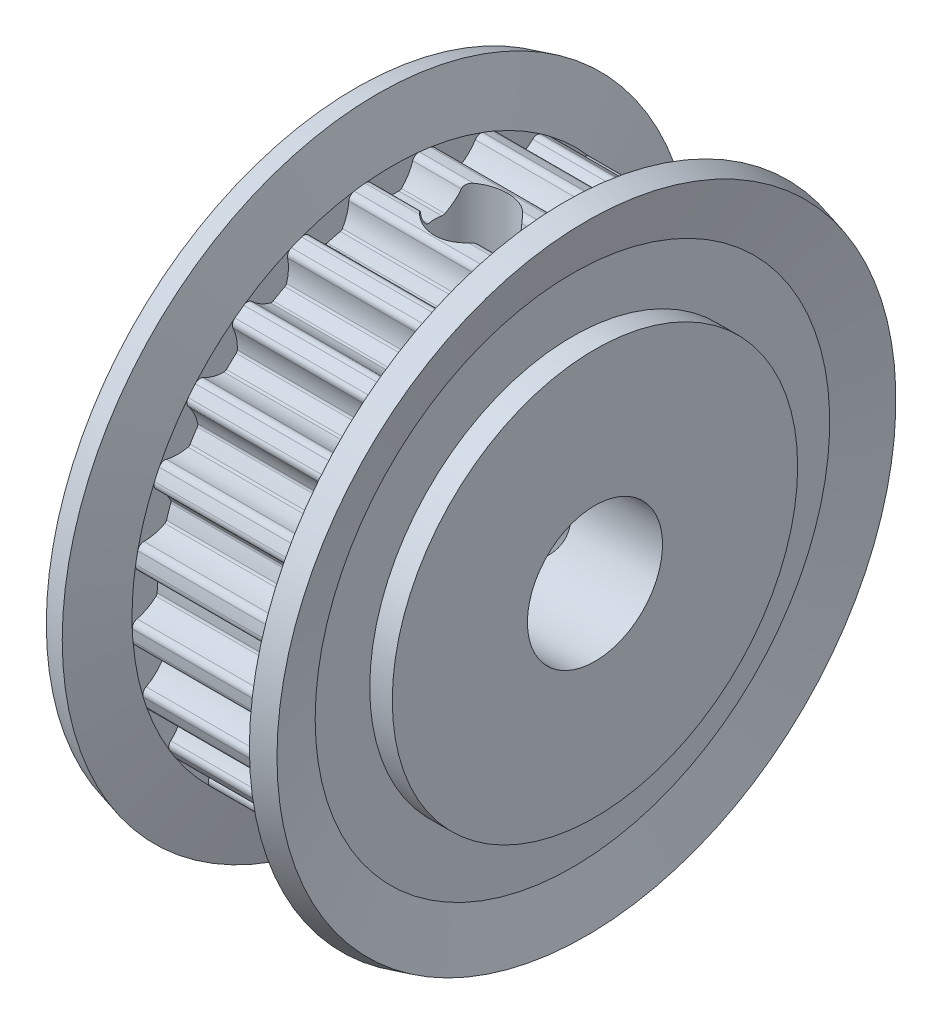
SolidWorks part; units mm, degrees
ref_plane "正面" through (0, 0, 0) normal (0, 0, 1) x (1, 0, 0)
ref_plane "平面" through (0, 0, 0) normal (0, 1, 0) x (1, 0, 0)
ref_plane "右側面" through (0, 0, 0) normal (1, 0, 0) x (0, 0, -1)
ref_plane "平面1" through (0, 0, 0) normal (0, 0, 1) x (1, 0, 0)
sketch "ｽｹｯﾁ1" plane through (0, 0, 0) normal (0, 0, 1) x (1, 0, 0)
  line L0 (0, 0) -> (0, 9)
  line L1 (0, 9) -> (1, 9)
  line L2 (1, 9) -> (1, 11.4233)
  line L3 (1, 11.4233) -> (0.3789, 13.7412)
  line L4 (0.3789, 13.7412) -> (1.3449, 14)
  line L5 (1.3449, 14) -> (2, 11.555)
  line L6 (2, 11.555) -> (9, 11.555)
  line L7 (9, 11.555) -> (9.6551, 14)
  line L8 (9.6551, 14) -> (10.6211, 13.7412)
  line L9 (10.6211, 13.7412) -> (10, 11.4233)
  line L10 (10, 11.4233) -> (10, 9)
  line L11 (10, 9) -> (11, 9)
  line L12 (11, 9) -> (11, 0)
  line L13 (11, 0) -> (0, 0)
  line L14 (11, 0) -> (0, 0) construction
revolve "回転1" add sketch "ｽｹｯﾁ1" angle 360 about L14
ref_plane "平面2" through (0, 0, 0) normal (0, 0, 1) x (1, 0, 0)
sketch "ｽｹｯﾁ2" plane through (0, 0, 0) normal (0, 0, 1) x (1, 0, 0)
  line L0 (0, 0) -> (0, 3)
  line L1 (0, 3) -> (11, 3)
  line L2 (11, 3) -> (11, 0)
  line L3 (11, 0) -> (0, 0)
  line L4 (11, 0) -> (0, 0) construction
revolve "ｶｯﾄ - 回転1" cut sketch "ｽｹｯﾁ2" angle 360 about L4
ref_plane "平面3" through (2, 0, 0) normal (1, 0, 0) x (0, 0, -1)
sketch "ｽｹｯﾁ3" plane through (2, 0, 0) normal (1, 0, 0) x (0, 0, -1)
  circle A0 centre (0, 0) radius 16.555
  arc A1 (-11.333, -0.1964) -> (-11.545, -0.4798) centre (-11.2653, -0.4681) ccw
  arc A2 (-11.545, -0.4798) -> (-11.5141, -0.971) centre (0, 0) ccw
  arc A3 (-11.5141, -0.971) -> (-11.2682, -1.2255) centre (-11.2351, -0.9475) ccw
  arc A4 (-11.2682, -1.2255) -> (-10.3739, -1.5653) centre (-11.5017, -3.1867) cw
  arc A5 (-10.3739, -1.5653) -> (-10.3115, -1.6645) centre (-10.4596, -1.6884) cw
  arc A6 (-10.3115, -1.6645) -> (-10.2002, -2.2483) centre (0, 0) ccw
  arc A7 (-10.2002, -2.2483) -> (-10.2217, -2.3635) centre (-10.3466, -2.2806) cw
  arc A8 (-10.2217, -2.3635) -> (-10.9281, -3.0087) centre (-11.8671, -1.2712) cw
  arc A9 (-10.9281, -3.0087) -> (-11.063, -3.3358) centre (-10.7949, -3.255) ccw
  arc A10 (-11.063, -3.3358) -> (-10.9109, -3.8039) centre (0, 0) ccw
  arc A11 (-10.9109, -3.8039) -> (-10.6094, -3.9893) centre (-10.6465, -3.7118) ccw
  arc A12 (-10.6094, -3.9893) -> (-9.6588, -4.096) centre (-10.3479, -5.9469) cw
  arc A13 (-9.6588, -4.096) -> (-9.5736, -4.1766) centre (-9.7111, -4.2366) cw
  arc A14 (-9.5736, -4.1766) -> (-9.3206, -4.7143) centre (0, 0) ccw
  arc A15 (-9.3206, -4.7143) -> (-9.3128, -4.8313) centre (-9.4544, -4.782) cw
  arc A16 (-9.3128, -4.8313) -> (-9.8365, -5.6318) centre (-11.1782, -4.1825) cw
  arc A17 (-9.8365, -5.6318) -> (-9.8859, -5.9823) centre (-9.6463, -5.8373) ccw
  arc A18 (-9.8859, -5.9823) -> (-9.6221, -6.3979) centre (0, 0) ccw
  arc A19 (-9.6221, -6.3979) -> (-9.284, -6.5024) centre (-9.389, -6.2428) ccw
  arc A20 (-9.284, -6.5024) -> (-8.3367, -6.3694) centre (-8.5439, -8.3335) cw
  arc A21 (-8.3367, -6.3694) -> (-8.2341, -6.4263) centre (-8.3524, -6.5185) cw
  arc A22 (-8.2341, -6.4263) -> (-7.8554, -6.8841) centre (0, 0) ccw
  arc A23 (-7.8554, -6.8841) -> (-7.8187, -6.9955) centre (-7.9682, -6.983) cw
  arc A24 (-7.8187, -6.9955) -> (-8.1269, -7.9012) centre (-9.7868, -6.831) cw
  arc A25 (-8.1269, -7.9012) -> (-8.0875, -8.2529) centre (-7.8916, -8.0529) ccw
  arc A26 (-8.0875, -8.2529) -> (-7.7287, -8.5898) centre (0, 0) ccw
  arc A27 (-7.7287, -8.5898) -> (-7.3753, -8.607) centre (-7.5415, -8.3816) ccw
  arc A28 (-7.3753, -8.607) -> (-6.4908, -8.2425) centre (-6.203, -10.1964) cw
  arc A29 (-6.4908, -8.2425) -> (-6.3773, -8.2721) centre (-6.4689, -8.3909) cw
  arc A30 (-6.3773, -8.2721) -> (-5.8966, -8.6214) centre (0, 0) ccw
  arc A31 (-5.8966, -8.6214) -> (-5.8333, -8.7201) centre (-5.9812, -8.7452) cw
  arc A32 (-5.8333, -8.7201) -> (-5.9066, -9.674) centre (-7.7806, -9.0503) cw
  arc A33 (-5.9066, -9.674) -> (-5.7811, -10.0049) centre (-5.641, -9.7624) ccw
  arc A34 (-5.7811, -10.0049) -> (-5.3497, -10.242) centre (0, 0) ccw
  arc A35 (-5.3497, -10.242) -> (-5.0031, -10.1707) centre (-5.2201, -9.9938) ccw
  arc A36 (-5.0031, -10.1707) -> (-4.237, -9.5977) centre (-3.4723, -11.4187) cw
  arc A37 (-4.237, -9.5977) -> (-4.1198, -9.5982) centre (-4.1789, -9.736) cw
  arc A38 (-4.1198, -9.5982) -> (-3.5672, -9.817) centre (0, 0) ccw
  arc A39 (-3.5672, -9.817) -> (-3.4815, -9.8969) centre (-3.6185, -9.9579) cw
  arc A40 (-3.4815, -9.8969) -> (-3.3152, -10.839) centre (-5.2854, -10.7009) cw
  arc A41 (-3.3152, -10.839) -> (-3.1113, -11.1282) centre (-3.0359, -10.8586) ccw
  arc A42 (-3.1113, -11.1282) -> (-2.6346, -11.2506) centre (0, 0) ccw
  arc A43 (-2.6346, -11.2506) -> (-2.3166, -11.0954) centre (-2.5707, -10.978) ccw
  arc A44 (-2.3166, -11.0954) -> (-1.717, -10.3499) centre (-0.5235, -11.9235) cw
  arc A45 (-1.717, -10.3499) -> (-1.6034, -10.3212) centre (-1.6264, -10.4694) cw
  arc A46 (-1.6034, -10.3212) -> (-1.0138, -10.3957) centre (0, 0) ccw
  arc A47 (-1.0138, -10.3957) -> (-0.9108, -10.4518) centre (-1.0284, -10.545) cw
  arc A48 (-0.9108, -10.4518) -> (-0.5155, -11.3229) centre (-2.4582, -11.6791) cw
  arc A49 (-0.5155, -11.3229) -> (-0.2461, -11.5524) centre (-0.2401, -11.2724) ccw
  arc A50 (-0.2461, -11.5524) -> (0.2461, -11.5524) centre (0, 0) ccw
  arc A51 (0.2461, -11.5524) -> (0.5155, -11.3229) centre (0.2401, -11.2724) ccw
  arc A52 (0.5155, -11.3229) -> (0.9108, -10.4518) centre (2.4582, -11.6791) cw
  arc A53 (0.9108, -10.4518) -> (1.0138, -10.3957) centre (1.0284, -10.545) cw
  arc A54 (1.0138, -10.3957) -> (1.6034, -10.3212) centre (0, 0) ccw
  arc A55 (1.6034, -10.3212) -> (1.717, -10.3499) centre (1.6264, -10.4694) cw
  arc A56 (1.717, -10.3499) -> (2.3166, -11.0954) centre (0.5235, -11.9235) cw
  arc A57 (2.3166, -11.0954) -> (2.6346, -11.2506) centre (2.5707, -10.978) ccw
  arc A58 (2.6346, -11.2506) -> (3.1113, -11.1282) centre (0, 0) ccw
  arc A59 (3.1113, -11.1282) -> (3.3152, -10.839) centre (3.0359, -10.8586) ccw
  arc A60 (3.3152, -10.839) -> (3.4815, -9.8969) centre (5.2854, -10.7009) cw
  arc A61 (3.4815, -9.8969) -> (3.5672, -9.817) centre (3.6185, -9.9579) cw
  arc A62 (3.5672, -9.817) -> (4.1198, -9.5982) centre (0, 0) ccw
  arc A63 (4.1198, -9.5982) -> (4.237, -9.5977) centre (4.1789, -9.736) cw
  arc A64 (4.237, -9.5977) -> (5.0031, -10.1707) centre (3.4723, -11.4187) cw
  arc A65 (5.0031, -10.1707) -> (5.3497, -10.242) centre (5.2201, -9.9938) ccw
  arc A66 (5.3497, -10.242) -> (5.7811, -10.0049) centre (0, 0) ccw
  arc A67 (5.7811, -10.0049) -> (5.9066, -9.674) centre (5.641, -9.7624) ccw
  arc A68 (5.9066, -9.674) -> (5.8333, -8.7201) centre (7.7806, -9.0503) cw
  arc A69 (5.8333, -8.7201) -> (5.8966, -8.6214) centre (5.9812, -8.7452) cw
  arc A70 (5.8966, -8.6214) -> (6.3773, -8.2721) centre (0, 0) ccw
  arc A71 (6.3773, -8.2721) -> (6.4908, -8.2425) centre (6.4689, -8.3909) cw
  arc A72 (6.4908, -8.2425) -> (7.3753, -8.607) centre (6.203, -10.1964) cw
  arc A73 (7.3753, -8.607) -> (7.7287, -8.5898) centre (7.5415, -8.3816) ccw
  arc A74 (7.7287, -8.5898) -> (8.0875, -8.2529) centre (0, 0) ccw
  arc A75 (8.0875, -8.2529) -> (8.1269, -7.9012) centre (7.8916, -8.0529) ccw
  arc A76 (8.1269, -7.9012) -> (7.8187, -6.9955) centre (9.7868, -6.831) cw
  arc A77 (7.8187, -6.9955) -> (7.8554, -6.8841) centre (7.9682, -6.983) cw
  arc A78 (7.8554, -6.8841) -> (8.2341, -6.4263) centre (0, 0) ccw
  arc A79 (8.2341, -6.4263) -> (8.3367, -6.3694) centre (8.3524, -6.5185) cw
  arc A80 (8.3367, -6.3694) -> (9.284, -6.5024) centre (8.5439, -8.3335) cw
  arc A81 (9.284, -6.5024) -> (9.6221, -6.3979) centre (9.389, -6.2428) ccw
  arc A82 (9.6221, -6.3979) -> (9.8859, -5.9823) centre (0, 0) ccw
  arc A83 (9.8859, -5.9823) -> (9.8365, -5.6318) centre (9.6463, -5.8373) ccw
  arc A84 (9.8365, -5.6318) -> (9.3128, -4.8313) centre (11.1782, -4.1825) cw
  arc A85 (9.3128, -4.8313) -> (9.3206, -4.7143) centre (9.4544, -4.782) cw
  arc A86 (9.3206, -4.7143) -> (9.5736, -4.1766) centre (0, 0) ccw
  arc A87 (9.5736, -4.1766) -> (9.6588, -4.096) centre (9.7111, -4.2366) cw
  arc A88 (9.6588, -4.096) -> (10.6094, -3.9893) centre (10.3479, -5.9469) cw
  arc A89 (10.6094, -3.9893) -> (10.9109, -3.8039) centre (10.6465, -3.7118) ccw
  arc A90 (10.9109, -3.8039) -> (11.063, -3.3358) centre (0, 0) ccw
  arc A91 (11.063, -3.3358) -> (10.9281, -3.0087) centre (10.7949, -3.255) ccw
  arc A92 (10.9281, -3.0087) -> (10.2217, -2.3635) centre (11.8671, -1.2712) cw
  arc A93 (10.2217, -2.3635) -> (10.2002, -2.2483) centre (10.3466, -2.2806) cw
  arc A94 (10.2002, -2.2483) -> (10.3115, -1.6645) centre (0, 0) ccw
  arc A95 (10.3115, -1.6645) -> (10.3739, -1.5653) centre (10.4596, -1.6884) cw
  arc A96 (10.3739, -1.5653) -> (11.2682, -1.2255) centre (11.5017, -3.1867) cw
  arc A97 (11.2682, -1.2255) -> (11.5141, -0.971) centre (11.2351, -0.9475) ccw
  arc A98 (11.5141, -0.971) -> (11.545, -0.4798) centre (0, 0) ccw
  arc A99 (11.545, -0.4798) -> (11.333, -0.1964) centre (11.2653, -0.4681) ccw
  arc A100 (11.333, -0.1964) -> (10.4883, 0.2528) centre (11.8104, 1.72) cw
  arc A101 (10.4883, 0.2528) -> (10.4388, 0.359) centre (10.5887, 0.3642) cw
  arc A102 (10.4388, 0.359) -> (10.4015, 0.9521) centre (0, 0) ccw
  arc A103 (10.4015, 0.9521) -> (10.4373, 1.0638) centre (10.5509, 0.9658) cw
  arc A104 (10.4373, 1.0638) -> (11.219, 1.6153) centre (11.9329, -0.2262) cw
  arc A105 (11.219, 1.6153) -> (11.3939, 1.923) centre (11.1178, 1.8764) ccw
  arc A106 (11.3939, 1.923) -> (11.3016, 2.4064) centre (0, 0) ccw
  arc A107 (11.3016, 2.4064) -> (11.0258, 2.6281) centre (11.0278, 2.3481) ccw
  arc A108 (11.0258, 2.6281) -> (10.096, 2.8532) centre (11.0116, 4.6031) cw
  arc A109 (10.096, 2.8532) -> (10.0216, 2.9438) centre (10.1655, 2.9861) cw
  arc A110 (10.0216, 2.9438) -> (9.8379, 3.509) centre (0, 0) ccw
  arc A111 (9.8379, 3.509) -> (9.8448, 3.626) centre (9.9792, 3.5594) cw
  arc A112 (9.8448, 3.626) -> (10.4648, 4.3546) centre (11.6142, 2.7485) cw
  arc A113 (10.4648, 4.3546) -> (10.5577, 4.6961) centre (10.3019, 4.5823) ccw
  arc A114 (10.5577, 4.6961) -> (10.3481, 5.1414) centre (0, 0) ccw
  arc A115 (10.3481, 5.1414) -> (10.0258, 5.2876) centre (10.0974, 5.0169) ccw
  arc A116 (10.0258, 5.2876) -> (9.0692, 5.2743) centre (9.5209, 7.1969) cw
  arc A117 (9.0692, 5.2743) -> (8.9746, 5.3436) centre (9.1035, 5.4203) cw
  arc A118 (8.9746, 5.3436) -> (8.6562, 5.8453) centre (0, 0) ccw
  arc A119 (8.6562, 5.8453) -> (8.6338, 5.9604) centre (8.7805, 5.9293) cw
  arc A120 (8.6338, 5.9604) -> (9.0531, 6.8203) centre (10.5658, 5.5505) cw
  arc A121 (9.0531, 6.8203) -> (9.0581, 7.1741) centre (8.8386, 7.0003) ccw
  arc A122 (9.0581, 7.1741) -> (8.7444, 7.5534) centre (0, 0) ccw
  arc A123 (8.7444, 7.5534) -> (8.3959, 7.6147) centre (8.5325, 7.3704) ccw
  arc A124 (8.3959, 7.6147) -> (7.4726, 7.364) centre (7.432, 9.3386) cw
  arc A125 (7.4726, 7.364) -> (7.3638, 7.4076) centre (7.4695, 7.514) cw
  arc A126 (7.3638, 7.4076) -> (6.9306, 7.8144) centre (0, 0) ccw
  arc A127 (6.9306, 7.8144) -> (6.8803, 7.9203) centre (7.0301, 7.9266) cw
  arc A128 (6.8803, 7.9203) -> (7.0725, 8.8574) centre (8.8535, 8.0037) cw
  arc A129 (7.0725, 8.8574) -> (6.9894, 9.2014) centre (6.8201, 8.9784) ccw
  arc A130 (6.9894, 9.2014) -> (6.5912, 9.4907) centre (0, 0) ccw
  arc A131 (6.5912, 9.4907) -> (6.2384, 9.4635) centre (6.4315, 9.2607) ccw
  arc A132 (6.2384, 9.4635) -> (5.4065, 8.991) centre (4.8761, 10.8935) cw
  arc A133 (5.4065, 8.991) -> (5.2903, 9.0062) centre (5.3662, 9.1355) cw
  arc A134 (5.2903, 9.0062) -> (4.7695, 9.2925) centre (0, 0) ccw
  arc A135 (4.7695, 9.2925) -> (4.6944, 9.3825) centre (4.838, 9.4259) cw
  arc A136 (4.6944, 9.3825) -> (4.6476, 10.338) centre (6.5849, 9.9541) cw
  arc A137 (4.6476, 10.338) -> (4.4815, 10.6505) centre (4.3729, 10.3925) ccw
  arc A138 (4.4815, 10.6505) -> (4.0239, 10.8317) centre (0, 0) ccw
  arc A139 (4.0239, 10.8317) -> (3.6889, 10.7176) centre (3.9264, 10.5693) ccw
  arc A140 (3.6889, 10.7176) -> (3.0007, 10.0531) centre (2.0138, 11.7639) cw
  arc A141 (3.0007, 10.0531) -> (2.8843, 10.0389) centre (2.9257, 10.183) cw
  arc A142 (2.8843, 10.0389) -> (2.3087, 10.1866) centre (0, 0) ccw
  arc A143 (2.3087, 10.1866) -> (2.2136, 10.2552) centre (2.3419, 10.3329) cw
  arc A144 (2.2136, 10.2552) -> (1.9306, 11.169) centre (3.9026, 11.2789) cw
  arc A145 (1.9306, 11.169) -> (1.6921, 11.4304) centre (1.6511, 11.1535) ccw
  arc A146 (1.6921, 11.4304) -> (1.2037, 11.4921) centre (0, 0) ccw
  arc A147 (1.2037, 11.4921) -> (0.9077, 11.2983) centre (1.1746, 11.2137) ccw
  arc A148 (0.9077, 11.2983) -> (0.4063, 10.4835) centre (-0.975, 11.8951) cw
  arc A149 (0.4063, 10.4835) -> (0.2971, 10.4408) centre (0.3014, 10.5907) cw
  arc A150 (0.2971, 10.4408) -> (-0.2971, 10.4408) centre (0, 0) ccw
  arc A151 (-0.2971, 10.4408) -> (-0.4063, 10.4835) centre (-0.3014, 10.5907) cw
  arc A152 (-0.4063, 10.4835) -> (-0.9077, 11.2983) centre (0.975, 11.8951) cw
  arc A153 (-0.9077, 11.2983) -> (-1.2037, 11.4921) centre (-1.1746, 11.2137) ccw
  arc A154 (-1.2037, 11.4921) -> (-1.6921, 11.4304) centre (0, 0) ccw
  arc A155 (-1.6921, 11.4304) -> (-1.9306, 11.169) centre (-1.6511, 11.1535) ccw
  arc A156 (-1.9306, 11.169) -> (-2.2136, 10.2552) centre (-3.9026, 11.2789) cw
  arc A157 (-2.2136, 10.2552) -> (-2.3087, 10.1866) centre (-2.3419, 10.3329) cw
  arc A158 (-2.3087, 10.1866) -> (-2.8843, 10.0389) centre (0, 0) ccw
  arc A159 (-2.8843, 10.0389) -> (-3.0007, 10.0531) centre (-2.9257, 10.183) cw
  arc A160 (-3.0007, 10.0531) -> (-3.6889, 10.7176) centre (-2.0138, 11.7639) cw
  arc A161 (-3.6889, 10.7176) -> (-4.0239, 10.8317) centre (-3.9264, 10.5693) ccw
  arc A162 (-4.0239, 10.8317) -> (-4.4815, 10.6505) centre (0, 0) ccw
  arc A163 (-4.4815, 10.6505) -> (-4.6476, 10.338) centre (-4.3729, 10.3925) ccw
  arc A164 (-4.6476, 10.338) -> (-4.6944, 9.3825) centre (-6.5849, 9.9541) cw
  arc A165 (-4.6944, 9.3825) -> (-4.7695, 9.2925) centre (-4.838, 9.4259) cw
  arc A166 (-4.7695, 9.2925) -> (-5.2903, 9.0062) centre (0, 0) ccw
  arc A167 (-5.2903, 9.0062) -> (-5.4065, 8.991) centre (-5.3662, 9.1355) cw
  arc A168 (-5.4065, 8.991) -> (-6.2384, 9.4635) centre (-4.8761, 10.8935) cw
  arc A169 (-6.2384, 9.4635) -> (-6.5912, 9.4907) centre (-6.4315, 9.2607) ccw
  arc A170 (-6.5912, 9.4907) -> (-6.9894, 9.2014) centre (0, 0) ccw
  arc A171 (-6.9894, 9.2014) -> (-7.0725, 8.8574) centre (-6.8201, 8.9784) ccw
  arc A172 (-7.0725, 8.8574) -> (-6.8803, 7.9203) centre (-8.8535, 8.0037) cw
  arc A173 (-6.8803, 7.9203) -> (-6.9306, 7.8144) centre (-7.0301, 7.9266) cw
  arc A174 (-6.9306, 7.8144) -> (-7.3638, 7.4076) centre (0, 0) ccw
  arc A175 (-7.3638, 7.4076) -> (-7.4726, 7.364) centre (-7.4695, 7.514) cw
  arc A176 (-7.4726, 7.364) -> (-8.3959, 7.6147) centre (-7.432, 9.3386) cw
  arc A177 (-8.3959, 7.6147) -> (-8.7444, 7.5534) centre (-8.5325, 7.3704) ccw
  arc A178 (-8.7444, 7.5534) -> (-9.0581, 7.1741) centre (0, 0) ccw
  arc A179 (-9.0581, 7.1741) -> (-9.0531, 6.8203) centre (-8.8386, 7.0003) ccw
  arc A180 (-9.0531, 6.8203) -> (-8.6338, 5.9604) centre (-10.5658, 5.5505) cw
  arc A181 (-8.6338, 5.9604) -> (-8.6562, 5.8453) centre (-8.7805, 5.9293) cw
  arc A182 (-8.6562, 5.8453) -> (-8.9746, 5.3436) centre (0, 0) ccw
  arc A183 (-8.9746, 5.3436) -> (-9.0692, 5.2743) centre (-9.1035, 5.4203) cw
  arc A184 (-9.0692, 5.2743) -> (-10.0258, 5.2876) centre (-9.5209, 7.1969) cw
  arc A185 (-10.0258, 5.2876) -> (-10.3481, 5.1414) centre (-10.0974, 5.0169) ccw
  arc A186 (-10.3481, 5.1414) -> (-10.5577, 4.6961) centre (0, 0) ccw
  arc A187 (-10.5577, 4.6961) -> (-10.4648, 4.3546) centre (-10.3019, 4.5823) ccw
  arc A188 (-10.4648, 4.3546) -> (-9.8448, 3.626) centre (-11.6142, 2.7485) cw
  arc A189 (-9.8448, 3.626) -> (-9.8379, 3.509) centre (-9.9792, 3.5594) cw
  arc A190 (-9.8379, 3.509) -> (-10.0216, 2.9438) centre (0, 0) ccw
  arc A191 (-10.0216, 2.9438) -> (-10.096, 2.8532) centre (-10.1655, 2.9861) cw
  arc A192 (-10.096, 2.8532) -> (-11.0258, 2.6281) centre (-11.0116, 4.6031) cw
  arc A193 (-11.0258, 2.6281) -> (-11.3016, 2.4064) centre (-11.0278, 2.3481) ccw
  arc A194 (-11.3016, 2.4064) -> (-11.3939, 1.923) centre (0, 0) ccw
  arc A195 (-11.3939, 1.923) -> (-11.219, 1.6153) centre (-11.1178, 1.8764) ccw
  arc A196 (-11.219, 1.6153) -> (-10.4373, 1.0638) centre (-11.9329, -0.2262) cw
  arc A197 (-10.4373, 1.0638) -> (-10.4015, 0.9521) centre (-10.5509, 0.9658) cw
  arc A198 (-10.4015, 0.9521) -> (-10.4388, 0.359) centre (0, 0) ccw
  arc A199 (-10.4388, 0.359) -> (-10.4883, 0.2528) centre (-10.5887, 0.3642) cw
  arc A200 (-10.4883, 0.2528) -> (-11.333, -0.1964) centre (-11.8104, 1.72) cw
extrude "ｶｯﾄ - 押し出し1" cut sketch "ｽｹｯﾁ3" along normal blind 7
ref_plane "平面4" through (5.5, 0, 0) normal (1, 0, 0) x (0, 0, -1)
sketch "ｽｹｯﾁ4" plane through (5.5, 0, 0) normal (1, 0, 0) x (0, 0, -1)
  line L0 (0, 11.555) -> (1.621, 11.555)
  line L1 (1.621, 11.555) -> (1.621, 0)
  line L2 (1.621, 0) -> (0, 0)
  line L3 (0, 0) -> (0, 11.555)
  line L4 (0, 0) -> (0, 11.555) construction
revolve "ｶｯﾄ - 回転2" cut sketch "ｽｹｯﾁ4" angle 360 about L4
ref_plane "平面5" through (5.5, 0, 0) normal (1, 0, 0) x (0, 0, -1)
sketch "ｽｹｯﾁ5" plane through (5.5, 0, 0) normal (1, 0, 0) x (0, 0, -1)
  line L0 (10.4553, -4.9199) -> (9.7651, -6.3866)
  line L1 (9.7651, -6.3866) -> (-0.6902, -1.4667)
  line L2 (-0.6902, -1.4667) -> (0, 0)
  line L3 (0, 0) -> (10.4553, -4.9199)
  line L4 (0, 0) -> (10.4553, -4.9199) construction
revolve "ｶｯﾄ - 回転3" cut sketch "ｽｹｯﾁ5" angle 360 about L4
